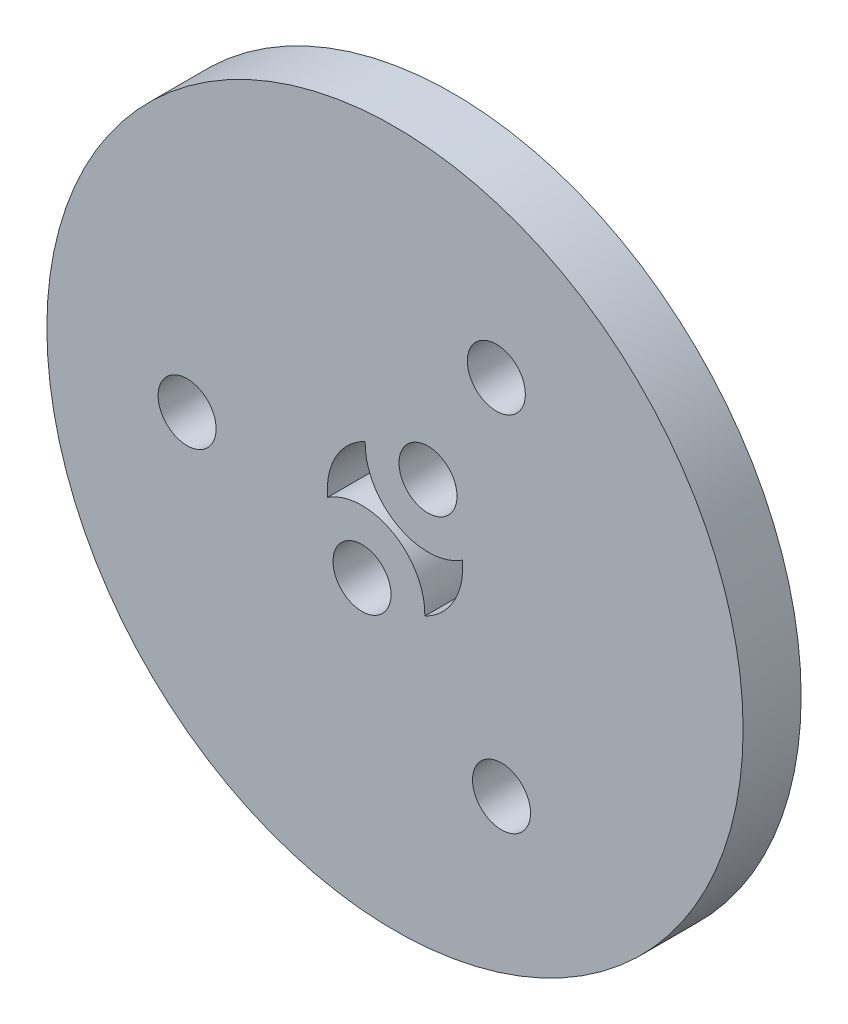
SolidWorks part; units mm, degrees
ref_plane "Plan de face" through (0, 0, 0) normal (0, 0, 1) x (1, 0, 0)
ref_plane "Plan de dessus" through (0, 0, 0) normal (0, 1, 0) x (1, 0, 0)
ref_plane "Plan de droite" through (0, 0, 0) normal (1, 0, 0) x (0, 0, -1)
sketch "Esquisse1" plane through (0, 0, 0) normal (0, 0, 1) x (1, 0, 0)
  line L0 (5.2405, 9.3862) -> (0, 0) construction
  line L1 (0, 0) -> (-5.2896, -9.4743) construction
  circle A0 centre (0, 0) radius 18
  circle A9 centre (5.2405, 9.3862) radius 1.5
  circle A19 centre (0, 0) radius 7.75 construction
  circle A21 centre (0, 0) radius 9 construction
  circle A33 centre (-1.7062, -3.056) radius 1.5
  circle A34 centre (1.7062, 3.056) radius 1.5
  arc A35 (1.5427, -3.1417) -> (-3.4839, -0.3353) centre (-1.7062, -3.056) ccw
  circle A36 centre (5.5084, -9.2314) radius 1.5
  circle A40 centre (-10.7489, -0.1547) radius 1.5
  arc A43 (-1.5427, 3.1417) -> (3.4839, 0.3353) centre (1.7062, 3.056) ccw
  arc A44 (1.5427, -3.1417) -> (3.4839, 0.3353) centre (0, 0) ccw
  arc A46 (-1.5427, 3.1417) -> (-3.4839, -0.3353) centre (0, 0) ccw
  point P3 (-1.7062, -3.056)
  point P14 (1.7062, 3.056)
  point P32 (0, 0)
  point P37 (0, 0)
  point P49 (0, 0)
  dimension "D1" = 36
  dimension "D2" = 10.7489
  dimension "D3" = 3
  dimension "D4" = 180
  dimension "D5" = 15.5
  dimension "D7" = 18
  dimension "D9" = 3.5
  dimension "D10" = 3
  dimension "D11" = 3
  dimension "D12" = 6.5
  dimension "D13" = 6.5
  dimension "D15" = 7
  dimension "D6" = 10.75
  dimension "D8" = 3.5
extrude "Boss.-Extru.1" add sketch "Esquisse1" along normal blind 3
